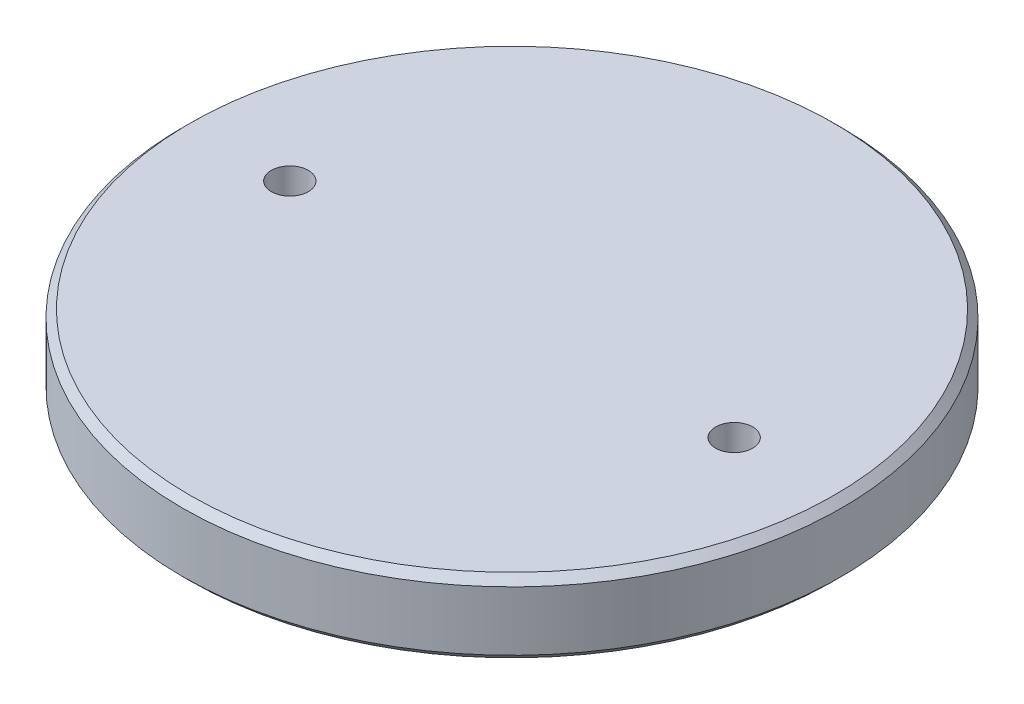
SolidWorks part; units mm, degrees
ref_plane "Front Plane" through (0, 0, 0) normal (0, 0, 1) x (1, 0, 0)
ref_plane "Top Plane" through (0, 0, 0) normal (0, 1, 0) x (1, 0, 0)
ref_plane "Right Plane" through (0, 0, 0) normal (1, 0, 0) x (0, 0, -1)
sketch "Sketch1" plane through (0, 0, 0) normal (0, 1, 0) x (1, 0, 0)
  circle A0 centre (0, 0) radius 56.515
  circle A1 centre (0, 0) radius 56.515 construction
extrude "Boss-Extrude1" add sketch "Sketch1" along normal blind 12.7
chamfer "Chamfer1" distance 1.27 angle 45 2 edges at (0, 0, 56.515) (0, 12.7, 56.515)
sketch "Sketch2" plane through (0, 0, 0) normal (0, -1, 0) x (1, 0, 0)
  circle A0 centre (0, 0) radius 50.165 construction
  circle A1 centre (0, 0) radius 50.165
extrude "Boss-Extrude2" add sketch "Sketch2" along normal blind 3.175
chamfer "Chamfer2" distance 1.27 angle 45 1 edges at (0, -3.175, -50.165)
sketch "Sketch3" plane through (0, 12.7, 0) normal (0, 1, 0) x (1, 0, 0)
  circle A0 centre (-38.1, 0) radius 3.175 construction
  circle A1 centre (38.1, 0) radius 3.175 construction
  circle A2 centre (-38.1, 0) radius 3.175
  circle A3 centre (38.1, 0) radius 3.175
extrude "Cut-Extrude1" cut sketch "Sketch3" against normal through all
